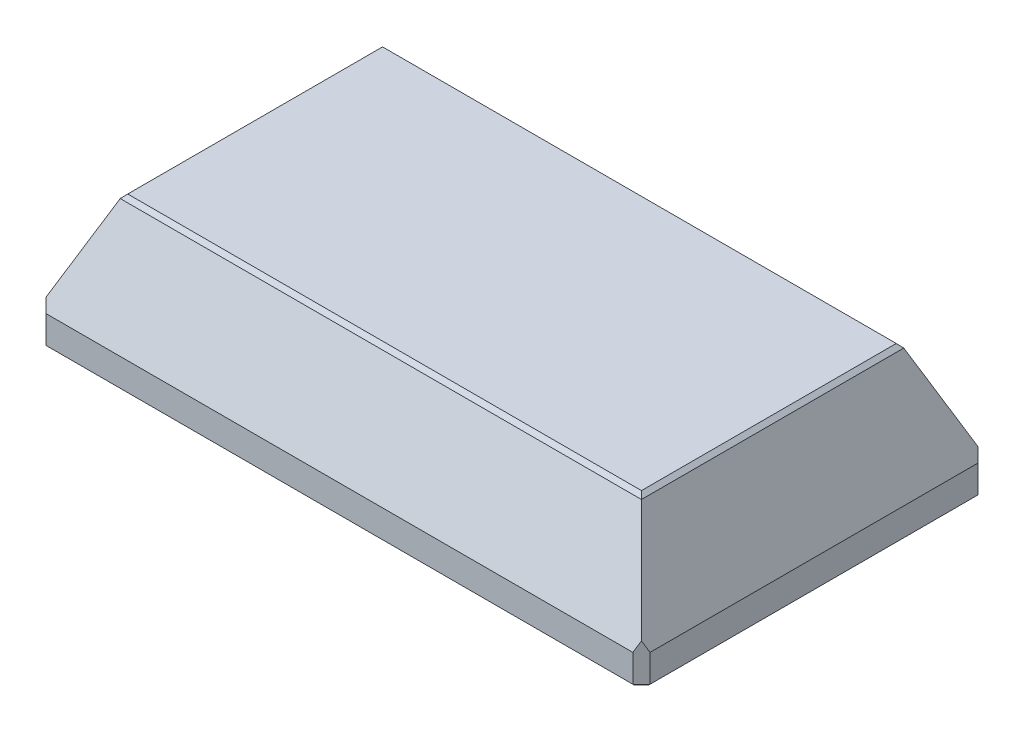
SolidWorks part; units mm, degrees
ref_plane "Front Plane" through (0, 0, 0) normal (0, 0, 1) x (1, 0, 0)
ref_plane "Top Plane" through (0, 0, 0) normal (0, 1, 0) x (1, 0, 0)
ref_plane "Right Plane" through (0, 0, 0) normal (1, 0, 0) x (0, 0, -1)
sketch "Sketch1" plane through (0, 0, 0) normal (0, 1, 0) x (1, 0, 0)
  line L1 (-70, -40) -> (70, -40)
  line L2 (-70, -40) -> (-70, 40)
  line L3 (-70, 40) -> (70, 40)
  line L4 (70, -40) -> (70, 40)
  line L5 (-70, -40) -> (70, 40) construction
  line L6 (-70, 40) -> (70, -40) construction
  point P0 (0, 0)
  dimension "D1" = 140
  dimension "D2" = 80
ref_plane "Plane1" through (0, 30, 0) normal (0, 1, 0) x (1, 0, 0)
sketch "Sketch2" plane through (0, 30, 0) normal (0, 1, 0) x (1, 0, 0)
  line L1 (-60, -30) -> (60, -30)
  line L2 (-60, -30) -> (-60, 30)
  line L3 (-60, 30) -> (60, 30)
  line L4 (60, -30) -> (60, 30)
  line L5 (-60, -30) -> (60, 30) construction
  line L6 (-60, 30) -> (60, -30) construction
  point P0 (0, 0)
  dimension "D1" = 60
  dimension "D2" = 120
extrude "Boss-Extrude1" add sketch "Sketch1" along normal blind 7
sketch "Sketch3" plane through (0, 7, 0) normal (0, 1, 0) x (1, 0, 0)
  line L4 (70, -40) -> (70, 40)
  line L5 (70, 40) -> (-70, 40)
  line L6 (-70, 40) -> (-70, -40)
  line L7 (-70, -40) -> (70, -40)
  line L8 (70, -40) -> (70, 40)
  line L9 (70, 40) -> (-70, 40)
  line L10 (-70, 40) -> (-70, -40)
  line L11 (-70, -40) -> (70, -40)
  dimension "D1" = 0
loft "Loft2" add profiles "Sketch3", "Sketch2"
chamfer "Chamfer1" distance 2 angle 45 4 edges at (-70, 3.5, 40) (70, 3.5, 40) (70, 3.5, -40) (-70, 3.5, -40)
sketch "Sketch4" plane through (0, 0, 0) normal (0, -1, 0) x (1, 0, 0)
  line L0 (0, 40) -> (0, -40) construction
  line L1 (-68, 40) -> (68, 40) construction
  line L2 (68, -40) -> (-68, -40) construction
  line L3 (-40, -36.5) -> (40, -36.5) construction
  circle A0 centre (40, -36.5) radius 2.05
  circle A1 centre (-40, -36.5) radius 2.05
  point P9 (0, -36.5)
  dimension "D3" = 4.1
  dimension "D1" = 3.5
  dimension "D2" = 80
extrude "Cut-Extrude1" cut sketch "Sketch4" against normal blind 7
sketch "Sketch5" plane through (0, 0, 0) normal (0, -1, 0) x (1, 0, 0)
  line L1 (-57, -25) -> (57, -25)
  line L2 (-57, -25) -> (-57, 25)
  line L3 (-57, 25) -> (57, 25)
  line L4 (57, -25) -> (57, 25)
  line L5 (-57, -25) -> (57, 25) construction
  line L6 (-57, 25) -> (57, -25) construction
  point P0 (0, 0)
  dimension "D1" = 50
  dimension "D2" = 114
extrude "Cut-Extrude2" cut sketch "Sketch5" against normal offset from surface (29 mm away) 1 up to face at (0, 30, 0)
mirror "Mirror1" about plane through (0, 0, 0) normal (0, 0, 1) of "Cut-Extrude1"
sketch "Sketch6" plane through (0, 0, 0) normal (0, -1, 0) x (1, 0, 0)
  line L0 (57, 25) -> (57, -25) construction
  line L1 (-57, -31) -> (57, -31)
  line L2 (-57, -31) -> (-57, 31)
  line L3 (-57, 31) -> (57, 31)
  line L4 (57, -31) -> (57, 31)
  line L5 (-57, -31) -> (57, 31) construction
  line L6 (-57, 31) -> (57, -31) construction
  line L7 (57, 25) -> (-57, 25) construction
  point P0 (0, 0)
  dimension "D1" = 6
extrude "Cut-Extrude3" cut sketch "Sketch6" against normal offset from surface (25 mm away) 4 up to face at (0, 29, 0)
sketch "Sketch7" plane through (0, 0, 0) normal (0, -1, 0) x (1, 0, 0)
  line L0 (-57, -31) -> (57, -31) construction
  line L1 (-57, 31) -> (-63, 31)
  line L2 (-57, 31) -> (-57, -31)
  line L3 (-57, -31) -> (-63, -31)
  line L4 (-63, 31) -> (-63, -31)
  line L5 (0, 40) -> (0, -40) construction
  line L6 (-68, 40) -> (68, 40) construction
  line L7 (68, -40) -> (-68, -40) construction
  line L8 (63, 31) -> (63, -31)
  line L9 (57, -31) -> (63, -31)
  line L10 (57, 31) -> (57, -31)
  line L11 (57, 31) -> (63, 31)
  dimension "D1" = 6
extrude "Cut-Extrude4" cut sketch "Sketch7" against normal blind 4
sketch "Sketch8" plane through (0, 4, 0) normal (0, -1, 0) x (1, 0, 0)
  line L0 (-63, 0) -> (63, 0) construction
  line L1 (-63, 31) -> (-63, -31) construction
  line L2 (63, -31) -> (63, 31) construction
  line L3 (-60, -25) -> (-60, 25) construction
  line L4 (-63, 31) -> (-57, -31) construction
  line L5 (0, 31) -> (0, -31) construction
  line L6 (-57, 31) -> (57, 31) construction
  line L7 (-63, -31) -> (63, -31) construction
  circle A0 centre (-60, 25) radius 2.05
  circle A1 centre (-60, -25) radius 2.05
  circle A2 centre (60, -25) radius 2.05
  circle A3 centre (60, 25) radius 2.05
  point P9 (-60, 0)
  dimension "D1" = 4.1
  dimension "D2" = 50
extrude "Cut-Extrude5" cut sketch "Sketch8" against normal blind 6
chamfer "Chamfer2" distance 1 angle 20 4 edges
chamfer "Chamfer3" distance 0.6 angle 45 8 edges at (69, 0, -39) (70, 0, 0) (69, 0, 39) (0, 0, -40) (-69, 0, -39) (-70, 0, 0) (-69, 0, 39) (0, 0, 40)
sketch "Skizze1" plane through (0, 29, 0) normal (0, -1, 0) x (1, 0, 0)
  line L0 (0, 25) -> (0, -25) construction
  line L1 (-57, 25) -> (57, 25) construction
  line L2 (-57, 25) -> (57, 25) construction
  line L3 (57, 0) -> (-57, 0) construction
  line L4 (57, 25) -> (57, -25) construction
  line L5 (-57, -31) -> (-57, 31) construction
  line L6 (-27.0252, -17.5) -> (27.0252, -17.5)
  line L7 (-27.0252, 25) -> (27.0252, 25)
  line L8 (-27.0252, 25) -> (-27.0252, 17.5)
  line L9 (-27.0252, 17.5) -> (27.0252, 17.5)
  line L10 (27.0252, 25) -> (27.0252, 17.5)
  line L11 (27.0252, -25) -> (27.0252, -17.5)
  line L12 (-27.0252, -25) -> (27.0252, -25)
  line L13 (-27.0252, -25) -> (-27.0252, -17.5)
  line L14 (57, 31) -> (57, -31) construction
  line L15 (57, 10.7265) -> (53, 10.7265)
  line L16 (57, 10.7265) -> (57, -10.7265)
  line L17 (57, -10.7265) -> (53, -10.7265)
  line L18 (53, 10.7265) -> (53, -10.7265)
  line L23 (-57, -25) -> (-57, 25) construction
  point P29 (0, 17.5)
  dimension "D1" = 35
  dimension "D2" = 110
extrude "Aufsatz-Linear austragen1" add sketch "Skizze1" along normal blind 10
sketch "Skizze3" plane through (0, 29, 0) normal (0, -1, 0) x (-1, 0, 0)
  line L0 (57, -25) -> (57, -31) construction
  line L2 (57, -28) -> (57, -25)
  line L10 (27.0252, -25) -> (27.0252, -28)
  line L11 (27.0252, -28) -> (57, -28)
  line L12 (27.0252, -25) -> (57, -25)
  line L14 (0, -39.4) -> (0, 39.4) construction
  line L22 (-67.7515, -39.4) -> (67.7515, -39.4) construction
  line L23 (67.7515, 39.4) -> (-67.7515, 39.4) construction
  line L24 (69.4, 0) -> (-69.4, 0) construction
  line L25 (69.4, -37.7515) -> (69.4, 37.7515) construction
  line L26 (-69.4, 37.7515) -> (-69.4, -37.7515) construction
  line L27 (-27.0252, -25) -> (-27.0252, -28)
  line L28 (-27.0252, -25) -> (-57, -25)
  line L29 (-27.0252, -28) -> (-57, -28)
  line L30 (-57, -28) -> (-57, -25)
  line L31 (27.0252, 25) -> (27.0252, 28)
  line L32 (27.0252, 28) -> (57, 28)
  line L33 (27.0252, 25) -> (57, 25)
  line L34 (57, 28) -> (57, 25)
  line L35 (-57, 28) -> (-57, 25)
  line L36 (-27.0252, 28) -> (-57, 28)
  line L37 (-27.0252, 25) -> (-27.0252, 28)
  line L38 (-27.0252, 25) -> (-57, 25)
extrude "Schnitt-Linear austragen2" cut sketch "Skizze3" along normal up to surface (4 mm away) up to face at (0, 25, 27)
